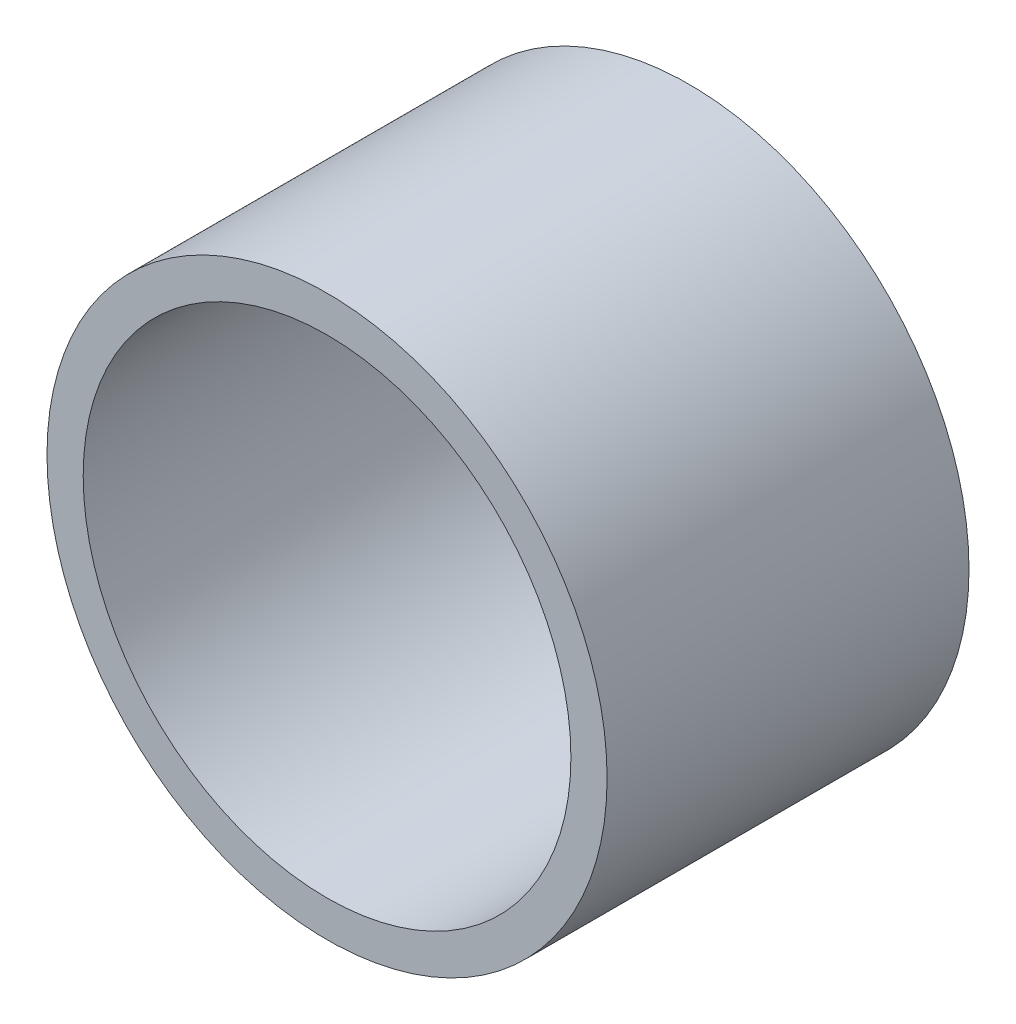
SolidWorks part; units mm, degrees
ref_plane "Front Plane" through (0, 0, 0) normal (0, 0, 1) x (1, 0, 0)
ref_plane "Top Plane" through (0, 0, 0) normal (0, 1, 0) x (1, 0, 0)
ref_plane "Right Plane" through (0, 0, 0) normal (1, 0, 0) x (0, 0, -1)
sketch "Sketch1" plane through (0, 0, 0) normal (0, 0, 1) x (1, 0, 0)
  circle A0 centre (0, 0) radius 8.5575
  circle A1 centre (0, 0) radius 9.8275
  dimension "D1" = 1.27
extrude "Extrude1" add sketch "Sketch1" along normal blind 12.7
